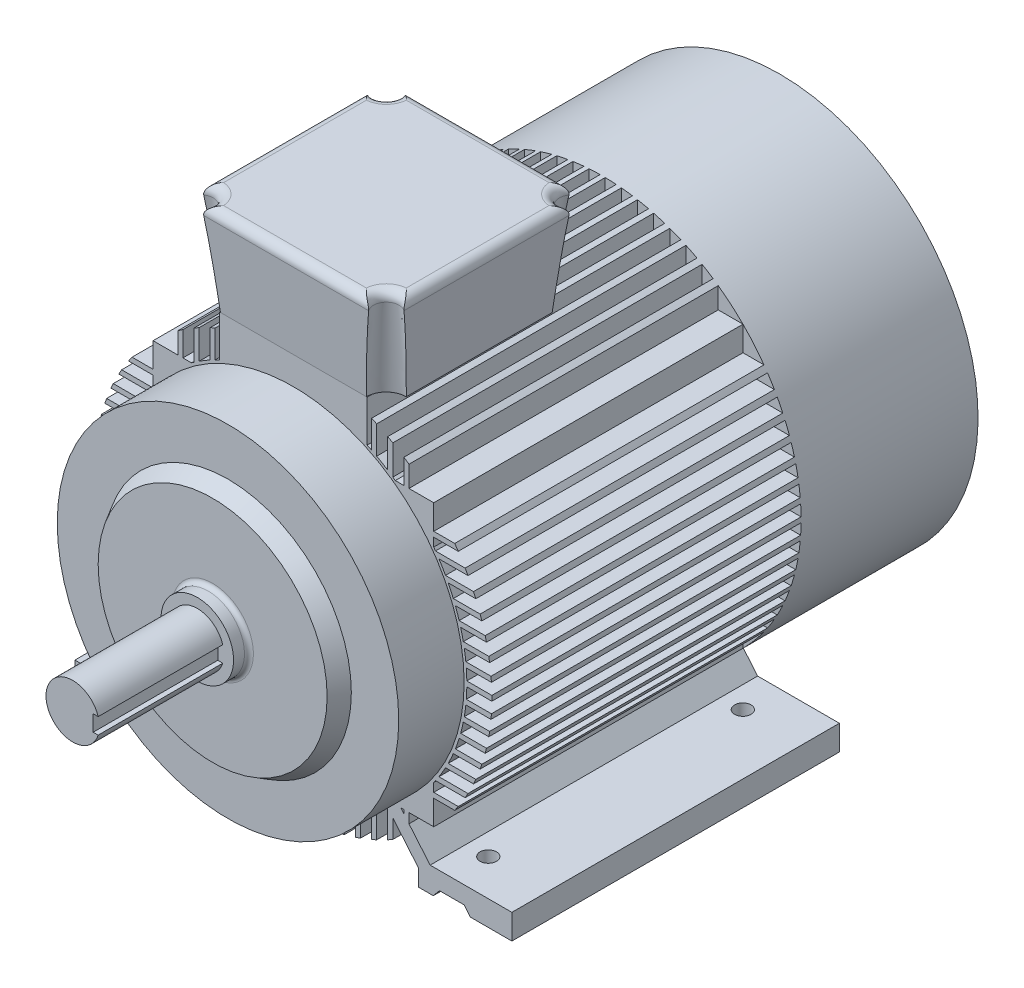
SolidWorks part; units mm, degrees
ref_plane "Front Plane" through (0, 0, 0) normal (0, 0, 1) x (1, 0, 0)
ref_plane "Shaft Plane" through (0, 0, 0) normal (0, 1, 0) x (1, 0, 0)
ref_plane "Right Plane" through (0, 0, 0) normal (1, 0, 0) x (0, 0, -1)
ref_axis "Shaft Axis" through (0, 0, -530.8576) along (0, 0, 1)
ref_plane "Foot Plane" through (0, -225, 0) normal (0, 1, 0) x (1, 0, 0)
ref_plane "Top Plane" through (0, 327, 0) normal (0, 1, 0) x (1, 0, 0)
ref_plane "Flange Plane" through (0, 0, 292) normal (0, 0, 1) x (1, 0, 0)
ref_plane "Shaft End Plane" through (0, 0, 432) normal (0, 0, 1) x (1, 0, 0)
sketch "Foot Section" plane through (0, 0, 0) normal (0, 0, 1) x (1, 0, 0)
  line L0 (153.654, -197) -> (215.5, -197)
  line L1 (215.5, -197) -> (215.5, -225)
  line L2 (215.5, -225) -> (198.8333, -225)
  line L3 (198.8333, -225) -> (191.7849, -216.6)
  line L4 (191.7849, -216.6) -> (164.2151, -216.6)
  line L5 (164.2151, -216.6) -> (157.1667, -225)
  line L6 (157.1667, -225) -> (140.5, -225)
  line L7 (140.5, -225) -> (140.5, -206.2152)
  line L8 (140.5, -206.2152) -> (105.1392, -164.0739)
  line L9 (153.654, -197) -> (118.2932, -154.8587)
  line L10 (0, -356.9971) -> (0, 0) construction
  line L11 (-153.654, -197) -> (-118.2932, -154.8587)
  line L12 (-140.5, -206.2152) -> (-105.1392, -164.0739)
  line L13 (-140.5, -225) -> (-140.5, -206.2152)
  line L14 (-157.1667, -225) -> (-140.5, -225)
  line L15 (-164.2151, -216.6) -> (-157.1667, -225)
  line L16 (-191.7849, -216.6) -> (-164.2151, -216.6)
  line L17 (-198.8333, -225) -> (-191.7849, -216.6)
  line L18 (-215.5, -225) -> (-198.8333, -225)
  line L19 (-215.5, -197) -> (-215.5, -225)
  line L20 (-153.654, -197) -> (-215.5, -197)
  line L21 (178, -216.6) -> (178, -356.9971) construction
  line L22 (-178, -216.6) -> (-178, -356.9971) construction
  line L25 (298.1, -225) -> (-298.1, -225) construction
  arc A0 (-118.2932, -154.8587) -> (-105.1392, -164.0739) centre (0, 0) ccw
  circle A1 centre (0, 0) radius 223 construction
  arc A2 (105.1392, -164.0739) -> (118.2932, -154.8587) centre (0, 0) ccw
  dimension "AC" = 446
  dimension "D1" = 389.7409
  dimension "AA" = 75
  dimension "AB" = 431
  dimension "HA" = 28
  dimension "D2" = 16
  dimension "D3" = 50
  dimension "D4" = 130
  dimension "D5" = 130
  dimension "D6" = 19.6
  dimension "A" = 356
  dimension "D8" = 16.6667
extrude "Foot" add sketch "Foot Section" along normal mid plane 368
sketch "Foot Hole Section" plane through (0, -225, 0) normal (0, 1, 0) x (1, 0, 0)
  line L0 (-533.2851, -292) -> (363.1586, -292) construction
  line L1 (-178, 143) -> (178, 143) construction
  line L2 (-178, 143) -> (-178, -143) construction
  line L3 (-178, -143) -> (178, -143) construction
  line L4 (178, 143) -> (178, -143) construction
  line L5 (-178, 143) -> (178, -143) construction
  line L6 (-178, -143) -> (178, 143) construction
  circle A0 centre (-178, -143) radius 9.25
  circle A1 centre (-178, 143) radius 9.25
  circle A2 centre (178, 143) radius 9.25
  circle A3 centre (178, -143) radius 9.25
  point P0 (0, 0)
  dimension "K" = 18.5
  dimension "B" = 286
  dimension "D1" = 356
  dimension "C" = 149
extrude "Foot Hole" cut sketch "Foot Hole Section" along normal up to surface (28 mm away) up to face at (-184.577, -197, 0)
sketch "Main Body Section" plane through (0, 0, 0) normal (0, 0, 1) x (1, 0, 0)
  circle A0 centre (0, 0) radius 273.5 construction
  circle A1 centre (0, 0) radius 173.2633
  circle A2 centre (0, 0) radius 194.8705
  arc A3 (105.1392, -164.0739) -> (118.2932, -154.8587) centre (0, 0) ccw construction
  dimension "D1" = 346.5265
extrude "Main Body" add sketch "Main Body Section" along normal blind 184 and the other way blind 234.671
sketch "Heat Sink Section" plane through (0, 0, 0) normal (0, 0, 1) x (1, 0, 0)
  line L0 (208.9156, 0) -> (287.6127, 0) construction
  line L1 (194.8495, 2.859) -> (222.9817, 2.859)
  line L2 (194.8495, -2.859) -> (222.9817, -2.859)
  line L3 (208.9156, 2.859) -> (208.9156, -2.859) construction
  line L4 (207.8719, 21.0041) -> (207.8719, 15.2862) construction
  line L5 (194.27, 15.2862) -> (222.4755, 15.2862)
  line L6 (193.7352, 21.0041) -> (222.0086, 21.0041)
  line L7 (207.8719, 18.1452) -> (287.6127, 18.1452) construction
  line L8 (205.217, 39.1493) -> (205.217, 33.4313) construction
  line L9 (191.9813, 33.4313) -> (220.4798, 33.4313)
  line L10 (190.8974, 39.1493) -> (219.5366, 39.1493)
  line L11 (205.217, 36.2903) -> (287.6127, 36.2903) construction
  line L12 (200.8858, 57.2945) -> (200.8858, 51.5765) construction
  line L13 (187.9211, 51.5765) -> (216.9536, 51.5765)
  line L14 (186.2574, 57.2945) -> (215.5141, 57.2945)
  line L15 (200.8858, 54.4355) -> (287.6127, 54.4355) construction
  line L16 (194.7639, 75.4396) -> (194.7639, 69.7217) construction
  line L17 (181.9708, 69.7217) -> (211.8204, 69.7217)
  line L18 (179.6757, 75.4396) -> (209.852, 75.4396)
  line L19 (194.7639, 72.5806) -> (287.6127, 72.5806) construction
  line L20 (186.6703, 93.5848) -> (186.6703, 87.8668) construction
  line L21 (173.9365, 87.8668) -> (204.9596, 87.8668)
  line L22 (170.928, 93.5848) -> (202.4127, 93.5848)
  line L23 (186.6703, 90.7258) -> (287.6127, 90.7258) construction
  line L24 (176.3247, 111.7299) -> (176.3247, 106.012) construction
  line L25 (163.5113, 106.012) -> (196.1899, 106.012)
  line L26 (159.6587, 111.7299) -> (192.9907, 111.7299)
  line L27 (176.3247, 108.871) -> (287.6127, 108.871) construction
  line L28 (287.6127, 0) -> (287.6127, 18.1452) construction
  line L29 (287.6127, 18.1452) -> (287.6127, 36.2903) construction
  line L30 (287.6127, 36.2903) -> (287.6127, 54.4355) construction
  line L31 (287.6127, 54.4355) -> (287.6127, 72.5806) construction
  line L32 (287.6127, 72.5806) -> (287.6127, 90.7258) construction
  line L33 (287.6127, 90.7258) -> (287.6127, 108.871) construction
  line L34 (0, 0) -> (157.6848, 157.6848) construction
  line L35 (0, 0) -> (159.7364, 0) construction
  line L36 (157.6848, 157.6848) -> (157.6848, 129.8751)
  line L37 (157.6848, 157.6848) -> (114.4989, 157.6848)
  line L38 (171.4626, 124.1572) -> (171.4626, 129.8751) construction
  line L39 (157.6848, 129.8751) -> (181.2773, 129.8751)
  line L40 (157.6848, 124.1572) -> (185.2404, 124.1572)
  line L41 (171.4626, 127.0161) -> (287.6127, 127.0161) construction
  line L42 (287.6127, 127.0161) -> (287.6127, 108.871) construction
  line L43 (157.6848, 124.1572) -> (157.6848, 114.4989)
  line L44 (167.7193, -127.0161) -> (287.6127, -127.0161) construction
  line L45 (150.1982, -124.1572) -> (185.2404, -124.1572)
  line L46 (145.2823, -129.8751) -> (181.2773, -129.8751)
  line L47 (167.7193, -124.1572) -> (167.7193, -129.8751) construction
  line L48 (179.8506, -108.871) -> (287.6127, -108.871) construction
  line L49 (163.5113, -106.012) -> (196.1899, -106.012)
  line L50 (159.6587, -111.7299) -> (192.9907, -111.7299)
  line L51 (179.8506, -106.012) -> (179.8506, -111.7299) construction
  line L52 (196.8956, -72.5806) -> (287.6127, -72.5806) construction
  line L53 (181.9708, -69.7217) -> (211.8204, -69.7217)
  line L54 (179.6757, -75.4396) -> (209.852, -75.4396)
  line L55 (196.8956, -69.7217) -> (196.8956, -75.4396) construction
  line L56 (202.4374, -54.4355) -> (287.6127, -54.4355) construction
  line L57 (187.9211, -51.5765) -> (216.9536, -51.5765)
  line L58 (186.2574, -57.2945) -> (215.5141, -57.2945)
  line L59 (202.4374, -51.5765) -> (202.4374, -57.2945) construction
  line L60 (206.2306, -36.2903) -> (287.6127, -36.2903) construction
  line L61 (191.9813, -33.4313) -> (220.4798, -33.4313)
  line L62 (190.8974, -39.1493) -> (219.5366, -39.1493)
  line L63 (206.2306, -33.4313) -> (206.2306, -39.1493) construction
  line L64 (189.448, -90.7258) -> (287.6127, -90.7258) construction
  line L65 (173.9365, -87.8668) -> (204.9596, -87.8668)
  line L66 (170.928, -93.5848) -> (202.4127, -93.5848)
  line L67 (189.448, -87.8668) -> (189.448, -93.5848) construction
  line L68 (208.3727, -18.1452) -> (287.6127, -18.1452) construction
  line L69 (194.27, -15.2862) -> (222.4755, -15.2862)
  line L70 (193.7352, -21.0041) -> (222.0086, -21.0041)
  line L71 (208.3727, -15.2862) -> (208.3727, -21.0041) construction
  line L72 (287.6127, 0) -> (287.6127, -18.1452) construction
  line L73 (287.6127, -18.1452) -> (287.6127, -36.2903) construction
  line L74 (287.6127, -36.2903) -> (287.6127, -54.4355) construction
  line L75 (287.6127, -54.4355) -> (287.6127, -72.5806) construction
  line L76 (287.6127, -72.5806) -> (287.6127, -90.7258) construction
  line L77 (287.6127, -90.7258) -> (287.6127, -108.871) construction
  line L78 (287.6127, -108.871) -> (287.6127, -127.0161) construction
  arc A0 (173.9365, 87.8668) -> (170.928, 93.5848) centre (0, 0) ccw
  arc A1 (118.2932, -154.8587) -> (-118.2932, -154.8587) centre (0, 0) ccw construction
  arc A2 (181.2773, -129.8751) -> (185.2404, -124.1572) centre (0, 0) ccw
  circle A3 centre (0, 0) radius 223 construction
  arc A4 (185.2404, 124.1572) -> (181.2773, 129.8751) centre (0, 0) ccw
  arc A5 (196.1899, 106.012) -> (192.9907, 111.7299) centre (0, 0) ccw
  arc A6 (204.9596, 87.8668) -> (202.4127, 93.5848) centre (0, 0) ccw
  arc A7 (211.8204, 69.7217) -> (209.852, 75.4396) centre (0, 0) ccw
  arc A8 (163.5113, 106.012) -> (159.6587, 111.7299) centre (0, 0) ccw
  arc A9 (157.6848, 114.4989) -> (114.4989, 157.6848) centre (0, 0) ccw
  arc A10 (145.2823, -129.8751) -> (150.1982, -124.1572) centre (0, 0) ccw
  arc A11 (181.9708, 69.7217) -> (179.6757, 75.4396) centre (0, 0) ccw
  arc A12 (187.9211, 51.5765) -> (186.2574, 57.2945) centre (0, 0) ccw
  arc A13 (216.9536, 51.5765) -> (215.5141, 57.2945) centre (0, 0) ccw
  arc A14 (191.9813, 33.4313) -> (190.8974, 39.1493) centre (0, 0) ccw
  arc A15 (220.4798, 33.4313) -> (219.5366, 39.1493) centre (0, 0) ccw
  arc A16 (194.27, 15.2862) -> (193.7352, 21.0041) centre (0, 0) ccw
  arc A17 (222.4755, 15.2862) -> (222.0086, 21.0041) centre (0, 0) ccw
  arc A18 (222.9817, -2.859) -> (222.9817, 2.859) centre (0, 0) ccw
  arc A19 (222.0086, -21.0041) -> (222.4755, -15.2862) centre (0, 0) ccw
  arc A20 (219.5366, -39.1493) -> (220.4798, -33.4313) centre (0, 0) ccw
  arc A21 (215.5141, -57.2945) -> (216.9536, -51.5765) centre (0, 0) ccw
  arc A22 (209.852, -75.4396) -> (211.8204, -69.7217) centre (0, 0) ccw
  arc A23 (202.4127, -93.5848) -> (204.9596, -87.8668) centre (0, 0) ccw
  arc A24 (192.9907, -111.7299) -> (196.1899, -106.012) centre (0, 0) ccw
  arc A25 (159.6587, -111.7299) -> (163.5113, -106.012) centre (0, 0) ccw
  arc A26 (170.928, -93.5848) -> (173.9365, -87.8668) centre (0, 0) ccw
  arc A27 (179.6757, -75.4396) -> (181.9708, -69.7217) centre (0, 0) ccw
  arc A28 (186.2574, -57.2945) -> (187.9211, -51.5765) centre (0, 0) ccw
  arc A29 (190.8974, -39.1493) -> (191.9813, -33.4313) centre (0, 0) ccw
  arc A30 (193.7352, -21.0041) -> (194.27, -15.2862) centre (0, 0) ccw
  arc A31 (194.8495, -2.859) -> (194.8495, 2.859) centre (0, 0) ccw
  dimension "D1" = 5.7179
  dimension "D2" = 18.1452
  dimension "D3" = 45
extrude "Heat Sink" add sketch "Heat Sink Section" along normal blind 184 and the other way blind 234.671
pattern_circular "Heat Sinks" count 4 over 360 about axis through (0, 0, 0) along (0, 0, 1) of "Heat Sink"
sketch "JB Base Section" plane through (0, 0, 184) normal (0, 0, 1) x (1, 0, 0)
  line L0 (82.8571, 223) -> (82.8571, 173.2633)
  line L1 (-82.8571, 223) -> (82.8571, 223)
  line L2 (-82.8571, 223) -> (82.8571, 173.2633) construction
  line L3 (-82.8571, 173.2633) -> (82.8571, 173.2633)
  line L4 (116, 223) -> (116, 173.2633) construction
  line L7 (-82.8571, 223) -> (-82.8571, 173.2633)
  line L8 (-82.8571, 198.1316) -> (0, 198.1316) construction
  line L9 (0, 198.1316) -> (82.8571, 198.1316) construction
  circle A0 centre (0, 0) radius 173.2633 construction
  arc A1 (2.859, 222.9817) -> (-2.859, 222.9817) centre (0, 0) ccw construction
  point P0 (0, 198.1316)
  dimension "AG" = 116
  dimension "D1" = 165.7143
extrude "JB Base" add sketch "JB Base Section" against normal blind 165.7143
sketch "JB Section" plane through (0, 223, 0) normal (0, 1, 0) x (1, 0, 0)
  line L0 (0, 24.8) -> (0, -184) construction
  line L1 (-81.9484, 24.8) -> (81.9484, 24.8)
  line L2 (-104.4, 2.3484) -> (-104.4, -161.5484)
  line L3 (-81.9484, -184) -> (81.9484, -184)
  line L4 (104.4, 2.3484) -> (104.4, -161.5484)
  line L5 (-81.9484, 24.8) -> (-104.4, 24.8) construction
  line L6 (-104.4, 24.8) -> (-104.4, 2.3484) construction
  line L7 (-104.4, -161.5484) -> (-104.4, -184) construction
  line L8 (-104.4, -184) -> (-81.9484, -184) construction
  line L9 (81.9484, 24.8) -> (104.4, 24.8) construction
  line L10 (104.4, 24.8) -> (104.4, 2.3484) construction
  line L11 (104.4, -161.5484) -> (104.4, -184) construction
  line L12 (104.4, -184) -> (81.9484, -184) construction
  line L13 (82.8571, -184) -> (-82.8571, -184) construction
  arc A0 (-104.4, 2.3484) -> (-81.9484, 24.8) centre (-104.4, 24.8) ccw
  arc A1 (-81.9484, -184) -> (-104.4, -161.5484) centre (-104.4, -184) ccw
  arc A2 (81.9484, 24.8) -> (104.4, 2.3484) centre (104.4, 24.8) ccw
  arc A3 (104.4, -161.5484) -> (81.9484, -184) centre (104.4, -184) ccw
  point P0 (0, -79.6)
  dimension "D1" = 104.4
  dimension "D2" = 22.4516
extrude "JB" add sketch "JB Section" against normal blind 0.1 and the other way up to surface (104 mm away) draft 5
fillet "JB Fillet" radius 10 8 edges at (-94.9582, 327, -15.3582) (94.9582, 327, -15.3582) (-94.9582, 327, 174.5582) (94.9582, 327, 174.5582) (0, 327, -33.8988) (-113.4988, 327, 79.6) (0, 327, 193.0988) (113.4988, 327, 79.6)
sketch "Back Cover Section" plane through (0, 0, 0) normal (1, 0, 0) x (0, 0, -1)
  line L0 (163.5, 223) -> (362.3267, 223)
  line L1 (362.3267, 223) -> (380, 157.0423)
  line L2 (380, 157.0423) -> (380, 0)
  line L3 (530.8576, 0) -> (-526.5731, 0) construction
  line L4 (380, 0) -> (163.5, 0) construction
  line L5 (163.5, 0) -> (163.5, 223)
  line L6 (-432, 247.5) -> (-432, -247.5) construction
  line L7 (184, -225) -> (184, -197) construction
  line L8 (380, 0) -> (163.5, 0)
  dimension "D1" = 446
  dimension "L" = 812
  dimension "D2" = 15
  dimension "D3" = 314.0845
  dimension "D4" = 20.5
revolve "Back Cover" add sketch "Back Cover Section" angle 360 about L4
sketch "End Sheild (Front) Section" plane through (0, 0, 184) normal (0, 0, 1) x (1, 0, 0)
  circle A0 centre (0, 0) radius 194.8705 construction
  arc A1 (186.2574, 57.2945) -> (181.9708, 69.7217) centre (0, 0) ccw construction
  circle A3 centre (0, 0) radius 191.8705
  dimension "D1" = 3
extrude "End Sheild (Front)" add sketch "End Sheild (Front) Section" along normal blind 73.4946
sketch "Sketch1" [suppressed] plane through (0, 0, 196.5) normal (0, 0, 1) x (1, 0, 0)
  line L0 (154.6848, 154.6848) -> (154.6848, 157.6848) construction
  line L1 (-154.6848, -154.6848) -> (154.6848, -154.6848)
  line L2 (-154.6848, -154.6848) -> (-154.6848, 154.6848)
  line L3 (-154.6848, 154.6848) -> (154.6848, 154.6848)
  line L4 (154.6848, -154.6848) -> (154.6848, 154.6848)
  line L5 (-154.6848, -154.6848) -> (154.6848, 154.6848) construction
  line L6 (-154.6848, 154.6848) -> (154.6848, -154.6848) construction
  line L7 (157.6848, 157.6848) -> (129.8751, 157.6848) construction
  line L8 (154.6848, 154.6848) -> (157.6848, 154.6848) construction
  point P0 (0, 0)
  dimension "D1" = 3
extrude "End Sheild (Front) Screw Hole" [suppressed] add sketch "Sketch1" along normal blind 30
sketch "Sketch3" plane through (0, 0, 0) normal (1, 0, 0) x (0, 0, -1)
  line L0 (-292, 40.7666) -> (-279.7473, 40.7666)
  line L1 (-292, 247.5) -> (-292, -247.5) construction
  line L2 (-274.7473, 45.7666) -> (-274.7473, 128.647)
  line L3 (-274.7473, 128.647) -> (-257.4946, 138.6079)
  line L4 (-257.4946, 191.8705) -> (-257.4946, -191.8705) construction
  line L5 (-257.4946, 138.6079) -> (-257.4946, 0)
  line L6 (-257.4946, 0) -> (-292, 0) construction
  line L7 (530.8576, 0) -> (-526.5731, 0) construction
  line L8 (-292, 0) -> (-292, 40.7666)
  line L9 (-274.7473, 45.7666) -> (-274.7473, 0) construction
  line L10 (-257.4946, 0) -> (-292, 0)
  arc A0 (-279.7473, 40.7666) -> (-274.7473, 45.7666) centre (-279.7473, 45.7666) ccw
  dimension "D3" = 5
  dimension "D1" = 138.6079
  dimension "D2" = 60
  dimension "D4" = 81.5333
revolve "End Sheild (Front) Seal Housing" add sketch "Sketch3" angle 360 about axis through (0, 0, -530.8576) along (0, 0, 1)
sketch "Shaft Section" plane through (0, 0, 292) normal (0, 0, 1) x (1, 0, 0)
  line L0 (28.6182, 9) -> (23, 9)
  line L1 (23, 9) -> (23, -9)
  line L2 (23, -9) -> (28.6182, -9)
  line L3 (0, 0) -> (23, 0) construction
  line L4 (23, 0) -> (30, 0) construction
  arc A0 (28.6182, 9) -> (28.6182, -9) centre (0, 0) ccw
  arc A1 (28.6182, -9) -> (28.6182, 9) centre (0, 0) ccw construction
  dimension "D" = 60
  dimension "F" = 18
  dimension "T1" = 7
extrude "Shaft" add sketch "Shaft Section" along normal up to surface (140 mm away) up to plane "Shaft End Plane"
sketch "Sketch5" [suppressed] plane through (0, 0, 0) normal (1, 0, 0) x (0, 0, -1)
  line L0 (-304.5, 225) -> (-288.5, 225)
  line L1 (-304.5, 245.3) -> (-304.5, -245.3) construction
  line L2 (-288.5, 225) -> (-288.5, 191.8705)
  line L3 (-269.9946, 0) -> (-304.5, 0) construction
  line L4 (530.8576, 0) -> (-526.5731, 0) construction
  line L5 (-304.5, 0) -> (-304.5, 70)
  line L6 (-304.5, 70) -> (-289.5, 85)
  line L7 (-289.5, 85) -> (-289.5, 145)
  line L8 (-289.5, 145) -> (-309.5, 145)
  line L9 (-309.5, 145) -> (-309.5, 175)
  line L10 (-309.5, 175) -> (-304.5, 175)
  line L11 (-304.5, 175) -> (-304.5, 225)
  line L12 (-269.9946, 0) -> (-304.5, 0)
  line L13 (-269.9946, 191.8705) -> (-288.5, 191.8705)
  line L14 (-269.9946, 191.8705) -> (-269.9946, 0)
  line L15 (-269.9946, 191.8705) -> (-269.9946, -191.8705) construction
  dimension "LA" = 16
  dimension "T" = 5
  dimension "P" = 450
  dimension "N" = 350
  dimension "D2" = 30
  dimension "D3" = 140
  dimension "D4" = 1
  dimension "D5" = 45
revolve "Flange" [suppressed] add sketch "Sketch5" angle 360 about axis through (0, 0, -530.8576) along (0, 0, 1)
sketch "Sketch6" plane through (0, 0, 292) normal (0, 0, 1) x (1, 0, 0)
  line L0 (-184.7759, 76.5367) -> (0, 0) construction
  line L1 (-157.058, 0) -> (0, 0) construction
  circle A0 centre (-184.7759, 76.5367) radius 8.75
  circle A1 centre (0, 0) radius 200 construction
  dimension "S" = 17.5
  dimension "M" = 400
  dimension "HAngle" = 22.5
extrude "Flange Hole" [suppressed] cut sketch "Sketch6" against normal up to surface (16 mm away)
pattern_circular "Flamge Holes" [suppressed] count 8 over 360 about axis through (0, 0, -530.8576) along (0, 0, 1)
sketch "Sketch7" plane through (215.5, 0, 0) normal (1, 0, 0) x (0, 0, -1)
  line L0 (-184, -225) -> (-184, -197)
  line L1 (-184, -197) -> (184, -197)
  line L2 (184, -197) -> (184, -225)
  line L3 (184, -225) -> (-184, -225)
extrude "Boss-Extrude1" add sketch "Sketch7" along normal blind 30
sketch "Sketch8" plane through (-215.5, 0, 0) normal (-1, 0, 0) x (0, 0, 1)
  line L0 (-184, -197) -> (184, -197)
  line L1 (184, -197) -> (184, -225)
  line L2 (184, -225) -> (-184, -225)
  line L3 (-184, -225) -> (-184, -197)
extrude "Boss-Extrude2" add sketch "Sketch8" along normal blind 30
equation "\"D1@Main Body Section\"=\"AC@Foot Section\"/ 1.2870588"
equation "\"D1@Foot Section\"=\"AC@Foot Section\" /1.14435"
equation "\"D2@Foot Section\"=\"HA@Foot Section\"/1.75"
equation "\"D6@Foot Section\"=\"HA@Foot Section\"*.7"
equation "\"D8@Foot Section\"=\"AA@Foot Section\"/4.5"
equation "\"D1@Foot Hole Section\" = \"A@Foot Section\""
equation "\"D1@Main Body\"=\"BB@Foot\"/2"
equation "\"D2@Main Body\"=\"BB@Foot\"*0.637693"
equation "\"D1@Heat Sink Section\"=\"AC@Foot Section\"/78"
equation "\"D2@Heat Sink Section\"=\"H@Foot Plane\"/12.4"
equation "\"D1@Heat Sink\" = \"D1@Main Body\""
equation "\"D2@Heat Sink\" = \"D2@Main Body\""
equation "\"D1@JB Base Section\" = \"AG@JB Base Section\" / .7"
equation "\"D1@JB Base\"=\"D1@JB Base Section\""
equation "\"D1@JB Section\" = \"AG@JB Base Section\" * .9"
equation "\"D2@JB Section\"=\"D1@JB Section\" / 4.65"
equation "\"D1@Flange Plane\"=\"B@Foot Hole Section\"/2+\"C@Foot Hole Section\""
equation "\"D1@Back Cover Section\" = \"AC@Foot Section\""
equation "\"D3@Back Cover Section\" = \"D1@Back Cover Section\" / 1.42"
equation "\"D4@Back Cover Section\" =  ( \"BB@Foot\" - \"B@Foot Hole Section\" )  / 4"
equation "\"D1@End Sheild (Front)\"=.76842*\"C@Foot Hole Section\"-( \"BB@Foot\" - \"B@Foot Hole Section\" ) / 2"
equation "\"D1@Sketch3\"=0.31078*\"AC@Foot Section\""
equation "\"D4@Sketch3\"=0.18281*\"AC@Foot Section\""
equation "\"D2@Sketch5\"=\"T@Sketch5\"*6"
equation "\"D3@Sketch5\" = \"N@Sketch5\" / 2.5"
